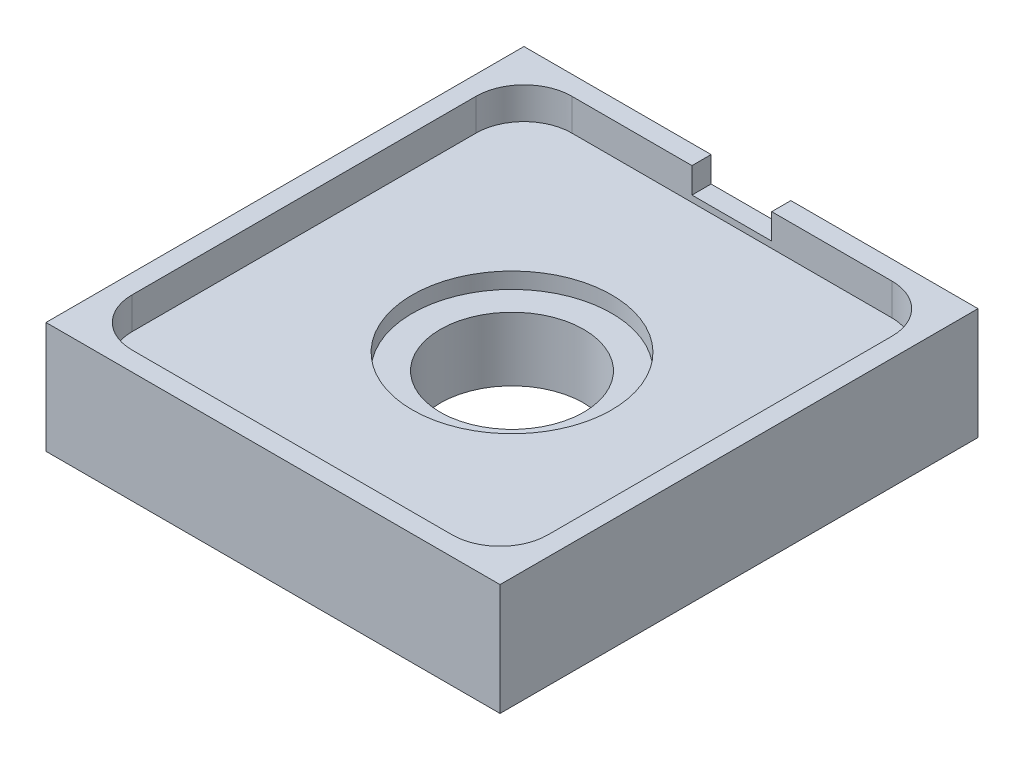
SolidWorks part; units mm, degrees
ref_plane "Front Plane" through (0, 0, 0) normal (0, 0, 1) x (1, 0, 0)
ref_plane "Top Plane" through (0, 0, 0) normal (0, 1, 0) x (1, 0, 0)
ref_plane "Right Plane" through (0, 0, 0) normal (1, 0, 0) x (0, 0, -1)
sketch "Sketch1" plane through (0, 0, 0) normal (0, 1, 0) x (1, 0, 0)
  line L1 (-14.235, 14.985) -> (14.235, 14.985)
  line L2 (-14.235, 14.985) -> (-14.235, -14.985)
  line L3 (-14.235, -14.985) -> (14.235, -14.985)
  line L4 (14.235, 14.985) -> (14.235, -14.985)
  line L5 (-14.235, 14.985) -> (14.235, -14.985) construction
  line L6 (-14.235, -14.985) -> (14.235, 14.985) construction
  point P0 (0, 0)
  dimension "D1" = 28.47
  dimension "D2" = 29.97
extrude "Boss-Extrude1" add sketch "Sketch1" against normal blind 5
sketch "Sketch2" plane through (0, 0, 0) normal (0, 1, 0) x (1, 0, 0)
  circle A0 centre (0, 0) radius 4.5
  dimension "D1" = 9
extrude "Cut-Extrude1" cut sketch "Sketch2" against normal up to next
sketch "Sketch4" plane through (0, 0, 0) normal (0, 1, 0) x (1, 0, 0)
  line L0 (-14.235, 14.985) -> (-14.235, -14.985) construction
  line L1 (-13.035, -13.785) -> (13.035, -13.785)
  line L2 (-13.035, -13.785) -> (-13.035, 13.785)
  line L3 (-13.035, 13.785) -> (13.035, 13.785)
  line L4 (13.035, -13.785) -> (13.035, 13.785)
  line L5 (-13.035, -13.785) -> (13.035, 13.785) construction
  line L6 (-13.035, 13.785) -> (13.035, -13.785) construction
  line L7 (14.235, 14.985) -> (-14.235, 14.985) construction
  line L12 (14.235, -14.985) -> (14.235, 14.985)
  line L13 (14.235, -14.985) -> (14.235, 14.985)
  line L14 (14.235, 14.985) -> (-14.235, 14.985)
  line L15 (14.235, 14.985) -> (-14.235, 14.985)
  line L20 (-14.235, 14.985) -> (-14.235, -14.985)
  line L21 (-14.235, 14.985) -> (-14.235, -14.985)
  line L22 (-14.235, -14.985) -> (14.235, -14.985)
  line L23 (-14.235, -14.985) -> (14.235, -14.985)
  point P0 (0, 0)
  dimension "D1" = 1.2
  dimension "D2" = 1.2
  dimension "D3" = 0
extrude "Boss-Extrude2" add sketch "Sketch4" along normal blind 2
sketch "Sketch7" plane through (0, 0, 0) normal (0, 1, 0) x (1, 0, 0)
  circle A0 centre (0, 0) radius 6.25
  dimension "D1" = 12.5
extrude "Cut-Extrude5" cut sketch "Sketch7" against normal blind 1
fillet "Fillet1" radius 3 4 edges at (13.035, 1, -13.785) (-13.035, 1, -13.785) (-13.035, 1, 13.785) (13.035, 1, 13.785)
sketch "Sketch8" plane through (0, 0, -14.985) normal (0, 0, -1) x (-1, 0, 0)
  line L0 (-14.235, 2) -> (14.235, 2) construction
  line L1 (2.5, 2) -> (-2.5, 2)
  line L2 (2.5, 2) -> (2.5, 0.4)
  line L3 (2.5, 0.4) -> (-2.5, 0.4)
  line L4 (-2.5, 2) -> (-2.5, 0.4)
  line L5 (14.235, 2) -> (2.5, 2) construction
  line L6 (-2.5, 2) -> (-14.235, 2) construction
  dimension "D1" = 1.6
  dimension "D2" = 5
extrude "Cut-Extrude6" cut sketch "Sketch8" against normal up to surface (1.2 mm away) up to face at (0, 1, -13.785)
